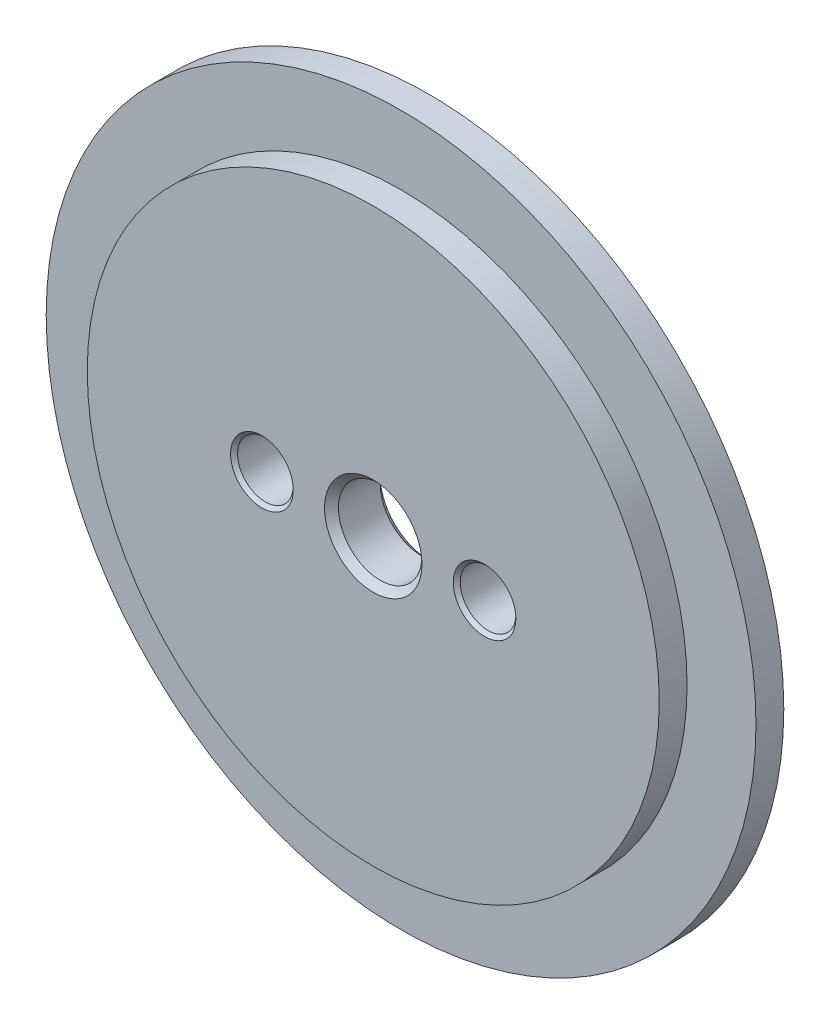
SolidWorks part; units mm, degrees
ref_plane "Front" through (0, 0, 0) normal (0, 0, 1) x (1, 0, 0)
ref_plane "Top" through (0, 0, 0) normal (0, 1, 0) x (1, 0, 0)
ref_plane "Right" through (0, 0, 0) normal (1, 0, 0) x (0, 0, -1)
sketch "Sketch1" plane through (0, 0, 0) normal (0, 0, 1) x (1, 0, 0)
  circle A0 centre (0, 0) radius 25.5
  dimension "D1" = 51
extrude "Boss-Extrude1" add sketch "Sketch1" along normal blind 2
sketch "Sketch2" plane through (0, 0, 2) normal (0, 0, 1) x (1, 0, 0)
  circle A0 centre (0, 0) radius 20.55
  circle A1 centre (0, 0) radius 25.5 construction
  dimension "D1" = 4.95
extrude "Boss-Extrude2" add sketch "Sketch2" along normal blind 2 contours A0
sketch "Sketch3" plane through (0, 0, 0) normal (0, 0, -1) x (-1, 0, 0)
  circle A5 centre (0, 0) radius 3
  circle A6 centre (8, 0) radius 2
  circle A7 centre (-8, 0) radius 2
  point P6 (0, 0)
  point P7 (0, 0)
  point P8 (0, 0)
  dimension "D1" = 6
  dimension "D2" = 4
  dimension "D3" = 4
  dimension "D4" = 8
  dimension "D5" = 8
extrude "Cut-Extrude1" cut sketch "Sketch3" against normal through all
chamfer "Chamfer1" distance 0.25 angle 45 2 edges at (6, 0, 0) (6, 0, 4)
chamfer "Chamfer2" distance 0.25 angle 45 2 edges at (-10, 0, 0) (-10, 0, 4)
chamfer "Chamfer3" distance 0.5 angle 45 2 edges at (-3, 0, 0) (-3, 0, 4)
